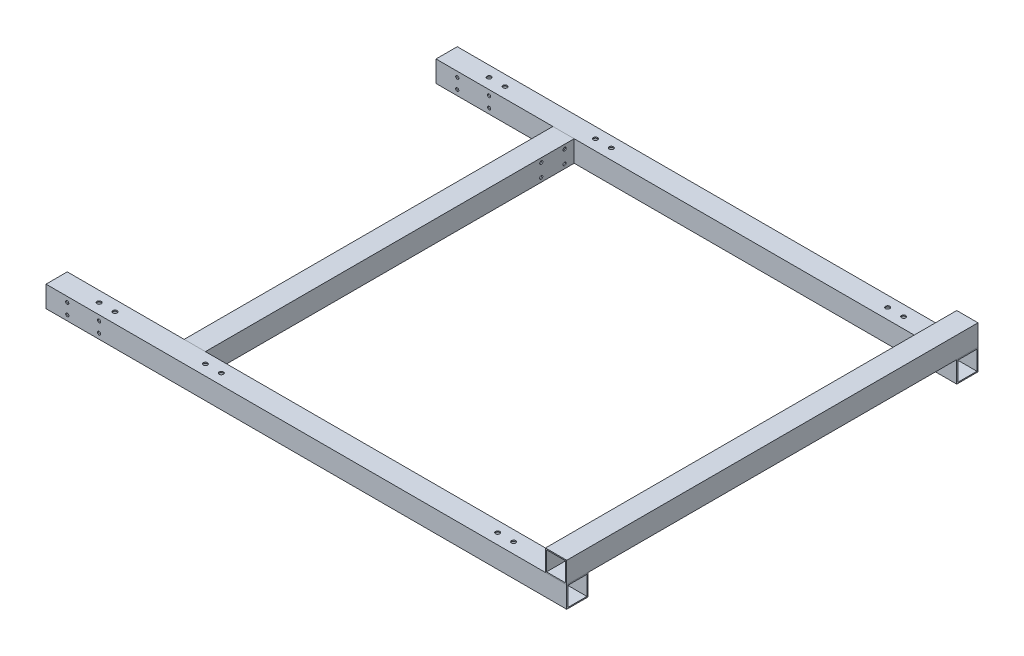
SolidWorks part; units mm, degrees
material "6063-O"
ref_plane "Front" through (0, 0, 0) normal (0, 0, 1) x (1, 0, 0)
ref_plane "Top" through (0, 0, 0) normal (0, 1, 0) x (1, 0, 0)
ref_plane "Right" through (0, 0, 0) normal (1, 0, 0) x (0, 0, -1)
sketch "草图1" plane through (0, 0, 0) normal (0, 1, 0) x (1, 0, 0)
  line L0 (0, 0) -> (500, 0)
  line L1 (0, -367) -> (500, -367)
  line L2 (0, -367) -> (0, -447)
  line L3 (0, -447) -> (500, -447)
  line L4 (130, 0) -> (130, -367)
  line L5 (130, -367) -> (130, -447)
  dimension "D1" = 447
  dimension "D2" = 80
  dimension "D3" = 500
  dimension "D4" = 130
other "铝管 20X20X1(1)"
ref_plane "基准面1" through (0, 0, 0) normal (1, 0, 0) x (0, 0, -1)
sketch "草图11" plane through (0, 0, 0) normal (1, 0, 0) x (0, 0, -1)
  line L1 (-10, -10) -> (10, -10)
  line L2 (-10, -10) -> (-10, 10)
  line L3 (-10, 10) -> (10, 10)
  line L4 (10, -10) -> (10, 10)
  line L5 (-10, -10) -> (10, 10) construction
  line L6 (-10, 10) -> (10, -10) construction
  line L7 (-9, -9) -> (9, -9)
  line L8 (-9, -9) -> (-9, 9)
  line L9 (-9, 9) -> (9, 9)
  line L10 (9, -9) -> (9, 9)
  line L11 (-9, -9) -> (9, 9) construction
  line L12 (-9, 9) -> (9, -9) construction
  point P0 (0, 0)
  point P6 (0, 0)
  point P11 (0, 0)
  dimension "D1" = 20
  dimension "D2" = 20
  dimension "D3" = 18
  dimension "D4" = 18
sketch "草图12" plane through (0, 0, 377) normal (0, 0, 1) x (1, 0, 0)
  line L0 (-10, -10) -> (-10, 10) construction
  line L1 (500, 10) -> (10, 10) construction
  circle A0 centre (30, 5) radius 1.5
  circle A1 centre (60, 5) radius 1.5
  circle A2 centre (30, -5) radius 1.5
  circle A3 centre (60, -5) radius 1.5
  dimension "D1" = 3
  dimension "D2" = 3
  dimension "D3" = 40
  dimension "D4" = 30
  dimension "D5" = 5
  dimension "D6" = 2
extrude "切除-拉伸1" cut sketch "草图12" against normal through all
sketch "草图13" plane through (0, 0, 0) normal (0, 1, 0) x (1, 0, 0)
  line L0 (500, 0) -> (650, 0)
  line L1 (500, 10) -> (500, -10) construction
  line L2 (500, -447) -> (650, -447)
  line L3 (500, -457) -> (500, -437) construction
  line L4 (500, -367) -> (650, -367)
  line L5 (500, -357) -> (500, -377) construction
  line L6 (650, -447) -> (650, 0)
  dimension "D1" = 150
other "铝管 20X20X1(2)"
ref_plane "基准面2" through (500, 0, 447) normal (1, 0, 0) x (0, 0, -1)
sketch "草图14" plane through (500, 0, 447) normal (1, 0, 0) x (0, 0, -1)
  line L1 (-10, -10) -> (10, -10)
  line L2 (-10, -10) -> (-10, 10)
  line L3 (-10, 10) -> (10, 10)
  line L4 (10, -10) -> (10, 10)
  line L5 (-10, -10) -> (10, 10) construction
  line L6 (-10, 10) -> (10, -10) construction
  line L7 (-9, -9) -> (9, -9)
  line L8 (-9, -9) -> (-9, 9)
  line L9 (-9, 9) -> (9, 9)
  line L10 (9, -9) -> (9, 9)
  line L11 (-9, -9) -> (9, 9) construction
  line L12 (-9, 9) -> (9, -9) construction
  point P0 (0, 0)
  point P6 (0, 0)
  point P11 (0, 0)
  dimension "D1" = 20
  dimension "D2" = 20
  dimension "D3" = 18
  dimension "D4" = 18
ref_plane "基准面3" through (0, 20, 0) normal (0, 1, 0) x (1, 0, 0)
sketch "草图15" plane through (0, 20, 0) normal (0, 1, 0) x (1, 0, 0)
  line L0 (490, 10) -> (490, -457)
  line L1 (500, 10) -> (0, 10) construction
  line L2 (-10, -457) -> (500, -457) construction
  dimension "D1" = 10
other "铝管 20X20X1(3)"
ref_plane "基准面4" through (490, 20, -10) normal (0, 0, 1) x (1, 0, 0)
sketch "草图16" plane through (490, 20, -10) normal (0, 0, 1) x (1, 0, 0)
  line L1 (-10, -10) -> (10, -10)
  line L2 (-10, -10) -> (-10, 10)
  line L3 (-10, 10) -> (10, 10)
  line L4 (10, -10) -> (10, 10)
  line L5 (-10, -10) -> (10, 10) construction
  line L6 (-10, 10) -> (10, -10) construction
  line L7 (-9, -9) -> (9, -9)
  line L8 (-9, -9) -> (-9, 9)
  line L9 (-9, 9) -> (9, 9)
  line L10 (9, -9) -> (9, 9)
  line L11 (-9, -9) -> (9, 9) construction
  line L12 (-9, 9) -> (9, -9) construction
  point P0 (0, 0)
  point P6 (0, 0)
  point P11 (0, 0)
  dimension "D1" = 20
  dimension "D2" = 20
  dimension "D3" = 18
  dimension "D4" = 18
sketch "草图17" plane through (140, 0, 0) normal (1, 0, 0) x (0, 0, -1)
  line L0 (-407, 10) -> (-407, -10) construction
  line L1 (-437, 10) -> (-377, 10) construction
  line L2 (-437, -10) -> (-377, -10) construction
  line L4 (-10, 0) -> (-81.1967, 0) construction
  line L5 (-10, 10) -> (-10, -10) construction
  line L6 (-30, 10) -> (-30, -10) construction
  line L7 (-357, 10) -> (-10, 10) construction
  line L8 (-357, -10) -> (-10, -10) construction
  circle A0 centre (-418, 6) radius 1.5 construction
  circle A1 centre (-418, -6) radius 1.5 construction
  circle A2 centre (-396, -6) radius 1.5 construction
  circle A3 centre (-396, 6) radius 1.5 construction
  circle A4 centre (-41, 6) radius 1.5
  circle A5 centre (-41, -6) radius 1.5
  circle A6 centre (-19, 6) radius 1.5
  circle A7 centre (-19, -6) radius 1.5
  dimension "D1" = 3
  dimension "D2" = 3
  dimension "D7" = 3
  dimension "D8" = 3
  dimension "D9" = 3
  dimension "D10" = 3
  dimension "D3" = 4
  dimension "D4" = 12
  dimension "D5" = 11
  dimension "D6" = 20
  dimension "D11" = 22
  dimension "D12" = 12
sketch "草图18" plane through (0, 0, 0) normal (0, 1, 0) x (1, 0, 0)
  line L0 (140, -100) -> (500, -100)
  line L1 (140, -357) -> (140, -10) construction
  line L2 (140, -297) -> (500, -297)
  line L3 (500, -357) -> (-10, -357) construction
  line L4 (500, -10) -> (0, -10) construction
  line L5 (500, 10) -> (500, -10) construction
  dimension "D1" = 60
  dimension "D2" = 90
other "铝管 20X20X1(4)"
ref_plane "基准面5" through (140, 0, 100) normal (1, 0, 0) x (0, 0, -1)
sketch "草图110" plane through (140, 0, 100) normal (1, 0, 0) x (0, 0, -1)
  line L1 (-10, -10) -> (10, -10)
  line L2 (-10, -10) -> (-10, 10)
  line L3 (-10, 10) -> (10, 10)
  line L4 (10, -10) -> (10, 10)
  line L5 (-10, -10) -> (10, 10) construction
  line L6 (-10, 10) -> (10, -10) construction
  line L7 (-9, -9) -> (9, -9)
  line L8 (-9, -9) -> (-9, 9)
  line L9 (-9, 9) -> (9, 9)
  line L10 (9, -9) -> (9, 9)
  line L11 (-9, -9) -> (9, 9) construction
  line L12 (-9, 9) -> (9, -9) construction
  point P0 (0, 0)
  point P6 (0, 0)
  point P11 (0, 0)
  dimension "D1" = 20
  dimension "D2" = 20
  dimension "D3" = 18
  dimension "D4" = 18
sketch "草图111" plane through (0, 10, 0) normal (0, 1, 0) x (1, 0, 0)
  line L0 (140, -100) -> (500, -100) construction
  line L1 (140, -90) -> (140, -110) construction
  line L2 (500, -90) -> (500, -110) construction
  line L3 (140, -297) -> (500, -297) construction
  line L4 (140, -287) -> (140, -307) construction
  line L5 (500, -287) -> (500, -307) construction
  line L6 (140, -357) -> (140, -10) construction
  circle A0 centre (160, -100) radius 6
  circle A1 centre (160, -297) radius 6
  circle A2 centre (180, -100) radius 6
  circle A3 centre (180, -297) radius 6
  circle A4 centre (200, -100) radius 6
  circle A5 centre (200, -297) radius 6
  circle A6 centre (220, -100) radius 6
  circle A7 centre (220, -297) radius 6
  circle A8 centre (240, -100) radius 6
  circle A9 centre (240, -297) radius 6
  circle A10 centre (260, -100) radius 6
  circle A11 centre (260, -297) radius 6
  circle A12 centre (280, -100) radius 6
  circle A13 centre (280, -297) radius 6
  circle A14 centre (300, -100) radius 6
  circle A15 centre (300, -297) radius 6
  circle A16 centre (320, -100) radius 6
  circle A17 centre (320, -297) radius 6
  circle A18 centre (340, -100) radius 6
  circle A19 centre (340, -297) radius 6
  circle A20 centre (360, -100) radius 6
  circle A21 centre (360, -297) radius 6
  circle A22 centre (380, -100) radius 6
  circle A23 centre (380, -297) radius 6
  circle A24 centre (400, -100) radius 6
  circle A25 centre (400, -297) radius 6
  circle A26 centre (420, -100) radius 6
  circle A27 centre (420, -297) radius 6
  circle A28 centre (440, -100) radius 6
  circle A29 centre (440, -297) radius 6
  dimension "D1" = 12
  dimension "D2" = 12
  dimension "D3" = 20
  dimension "D4" = 20
  dimension "D5" = 15
extrude "切除-拉伸3" cut sketch "草图111" against normal through all
extrude "切除-拉伸5" cut sketch "草图17" against normal through all
sketch "草图113" plane through (0, 0, 457) normal (0, 0, 1) x (1, 0, 0)
  line L0 (660, -10) -> (660, 10) construction
  line L1 (660, 10) -> (500, 10) construction
  line L2 (500, 10) -> (500, -10) construction
  line L3 (500, -10) -> (660, -10) construction
  line L4 (-10, 10) -> (-10, -10) construction
  line L5 (-10, -10) -> (500, -10) construction
  line L6 (500, -10) -> (500, 10) construction
  line L7 (500, 10) -> (-10, 10) construction
  line L8 (660, -10) -> (660, 10)
  line L9 (660, 10) -> (500, 10)
  line L10 (500, 10) -> (500, -10)
  line L11 (500, -10) -> (660, -10)
  line L12 (-10, 10) -> (-10, -10)
  line L13 (-10, -10) -> (500, -10)
  line L14 (500, -10) -> (500, 10)
  line L15 (500, 10) -> (-10, 10)
  line L17 (418.5326, 10) -> (518.891, 10)
  line L18 (418.5326, 10) -> (418.5326, 44.5746)
  line L19 (418.5326, 44.5746) -> (518.891, 44.5746)
  line L20 (518.891, 10) -> (518.891, 44.5746)
  line M1 (-10, 10) -> (-10, -10)
  line M2 (-10, -10) -> (500, -10)
  line M3 (500, -10) -> (500, 10)
  line M4 (500, 10) -> (-10, 10)
extrude "切除-拉伸7" cut sketch "草图113" against normal up to surface (80 mm away) contours L15 M4 M1 M2 M3 | L11 L8 L9 M3 | L15 L20 L19 L18 up to face at (31.5, 5, 377)
sketch "草图114" plane through (0, -10, 0) normal (0, -1, 0) x (1, 0, 0)
  circle A0 centre (50, 367) radius 2
  circle A1 centre (65, 367) radius 2
  circle A2 centre (150, 367) radius 2
  circle A3 centre (165, 367) radius 2
  circle A4 centre (425, 367) radius 2
  circle A5 centre (440, 367) radius 2
  dimension "D1" = 4
  dimension "D2" = 4
  dimension "D3" = 4
  dimension "D4" = 4
  dimension "D5" = 4
  dimension "D6" = 4
extrude "切除-拉伸8" cut sketch "草图114" against normal through all
sketch "草图115" plane through (0, -10, 0) normal (0, -1, 0) x (1, 0, 0)
  circle A0 centre (50, 0) radius 2
  circle A1 centre (65, 0) radius 2
  circle A2 centre (150, 0) radius 2
  circle A3 centre (165, 0) radius 2
  circle A4 centre (440, 0) radius 2
  circle A5 centre (425, 0) radius 2
  dimension "D1" = 4
  dimension "D2" = 4
  dimension "D3" = 4
  dimension "D4" = 4
  dimension "D5" = 4
  dimension "D6" = 4
extrude "切除-拉伸9" cut sketch "草图115" against normal through all
sketch "草图116" plane through (0, 0, 377) normal (0, 0, 1) x (1, 0, 0)
  line L0 (-10, 10) -> (10, 10)
  line L1 (10, 10) -> (10, -10)
  line L2 (10, -10) -> (-10, -10)
  line L3 (-10, -10) -> (-10, 10)
extrude "切除-拉伸10" cut sketch "草图116" against normal through all
sketch "草图117" plane through (500, 0, 0) normal (1, 0, 0) x (0, 0, -1)
  line L2 (-397.1065, 45.2565) -> (66.6872, 45.2565)
  line L3 (-397.1065, 45.2565) -> (-397.1065, -66.9857)
  line L4 (-397.1065, -66.9857) -> (66.6872, -66.9857)
  line L5 (66.6872, 45.2565) -> (66.6872, -66.9857)
extrude "切除-拉伸11" cut sketch "草图117" along normal blind 220
sketch "草图118" plane through (140, 0, 0) normal (1, 0, 0) x (0, 0, -1)
  line L0 (-357, 10) -> (-10, 10) construction
  line L1 (-318.6875, 10) -> (-69.0784, 10)
  line L2 (-318.6875, 10) -> (-318.6875, -10)
  line L3 (-318.6875, -10) -> (-69.0784, -10)
  line L4 (-69.0784, 10) -> (-69.0784, -10)
  line L5 (-357, -10) -> (-10, -10) construction
extrude "切除-拉伸12" cut sketch "草图118" along normal blind 393
